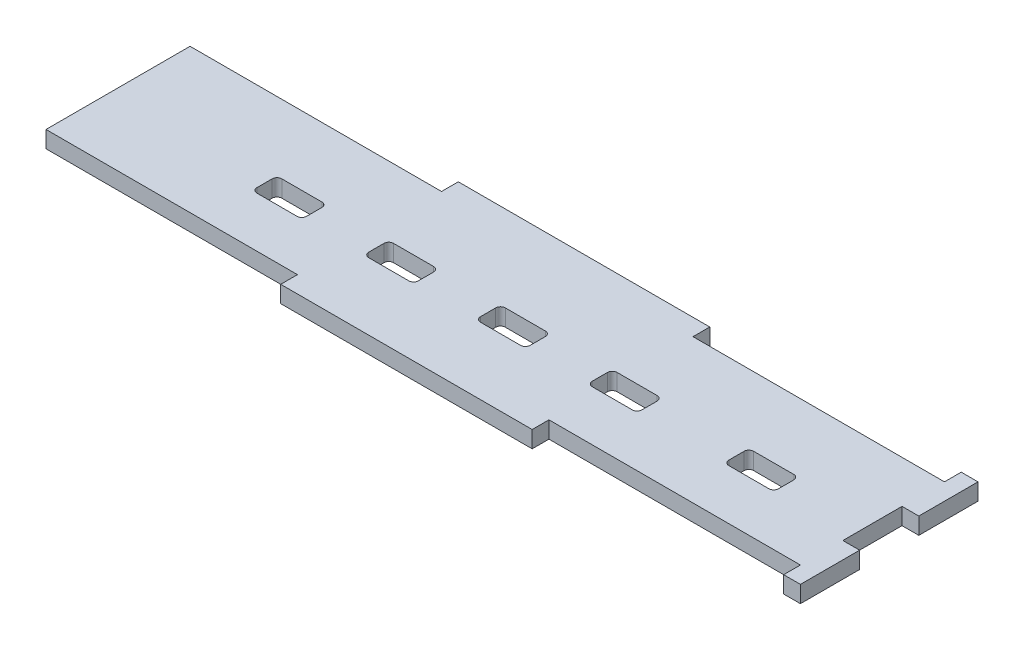
SolidWorks part; units mm, degrees
ref_plane "Front Plane" through (0, 0, 0) normal (0, 0, 1) x (1, 0, 0)
ref_plane "Top Plane" through (0, 0, 0) normal (0, 1, 0) x (1, 0, 0)
ref_plane "Right Plane" through (0, 0, 0) normal (1, 0, 0) x (0, 0, -1)
sketch "Sketch1" plane through (0, 0, 0) normal (0, 1, 0) x (1, 0, 0)
  line L6 (4, 2.8333) -> (4, 12.3667)
  line L8 (-117.5, 12.3667) -> (-117.5, 2.8333)
  line L11 (6.7, -6.7) -> (4, -6.7)
  line L12 (-117.5, 19.2) -> (-117.5, 12.3667)
  line L17 (6.7, -6.7) -> (6.7, 2.8333)
  line L18 (-117.5, -4) -> (-117.5, 2.8333)
  line L21 (-111.5, -4) -> (-117.5, -4) construction
  line L22 (4, -4) -> (-111.5, -4) construction
  line L23 (-117.5, -4) -> (-77, -4)
  line L25 (-120.2, 21.9) -> (-120.2, -6.7) construction
  line L28 (-36.5, -4) -> (4, -4)
  line L31 (-77, -4) -> (-77, -6.7)
  line L32 (-36.5, -4) -> (-36.5, -6.7)
  line L35 (-117.5, 19.2) -> (-117.5, -4) construction
  line L36 (-111.5, -6.7) -> (-120.2, -6.7) construction
  line L37 (6.7, -6.7) -> (-111.5, -6.7) construction
  line L39 (6.7, -6.7) -> (6.7, 21.9) construction
  line L40 (6.7, 12.3667) -> (6.7, 21.9)
  line L41 (6.7, 12.3667) -> (4, 12.3667)
  line L42 (6.7, 2.8333) -> (4, 2.8333)
  line L43 (4, -4) -> (4, -6.7)
  line L44 (4, 19.2) -> (4, 21.9)
  line L45 (4, -4) -> (4, 19.2) construction
  line L46 (-36.5, -6.7) -> (-77, -6.7)
  line L47 (4, 19.2) -> (-111.5, 19.2) construction
  line L48 (-111.5, 19.2) -> (-117.5, 19.2) construction
  line L49 (6.7, 21.9) -> (-111.5, 21.9) construction
  line L50 (-111.5, 21.9) -> (-120.2, 21.9) construction
  line L52 (6.7, 21.9) -> (4, 21.9)
  line L54 (-36.5, 19.2) -> (4, 19.2)
  line L55 (-36.5, 19.2) -> (-36.5, 21.9)
  line L56 (-36.5, 21.9) -> (-77, 21.9)
  line L57 (-77, 19.2) -> (-77, 21.9)
  line L58 (-117.5, 19.2) -> (-77, 19.2)
  line L59 (-91.6279, 8.1) -> (-85.1721, 8.1)
  line L60 (-92.4, 7.3279) -> (-92.4, 4.8721)
  line L61 (-91.6279, 4.1) -> (-85.1721, 4.1)
  line L62 (-84.4, 7.3279) -> (-84.4, 4.8721)
  line L63 (-92.4, 8.1) -> (-84.4, 4.1) construction
  line L64 (-92.4, 4.1) -> (-84.4, 8.1) construction
  line L65 (-73.6279, 8.1) -> (-67.1721, 8.1)
  line L66 (-74.4, 7.3279) -> (-74.4, 4.8721)
  line L67 (-73.6279, 4.1) -> (-67.1721, 4.1)
  line L68 (-66.4, 7.3279) -> (-66.4, 4.8721)
  line L69 (-74.4, 8.1) -> (-66.4, 4.1) construction
  line L70 (-74.4, 4.1) -> (-66.4, 8.1) construction
  line L71 (-55.6279, 8.1) -> (-49.1721, 8.1)
  line L72 (-56.4, 7.3279) -> (-56.4, 4.8721)
  line L73 (-55.6279, 4.1) -> (-49.1721, 4.1)
  line L74 (-48.4, 7.3279) -> (-48.4, 4.8721)
  line L75 (-56.4, 8.1) -> (-48.4, 4.1) construction
  line L76 (-56.4, 4.1) -> (-48.4, 8.1) construction
  line L77 (-37.6279, 8.1) -> (-31.1721, 8.1)
  line L78 (-38.4, 7.3279) -> (-38.4, 4.8721)
  line L79 (-37.6279, 4.1) -> (-31.1721, 4.1)
  line L80 (-30.4, 7.3279) -> (-30.4, 4.8721)
  line L81 (-38.4, 8.1) -> (-30.4, 4.1) construction
  line L82 (-38.4, 4.1) -> (-30.4, 8.1) construction
  line L83 (-15.6279, 8.1) -> (-9.1721, 8.1)
  line L84 (-16.4, 7.3279) -> (-16.4, 4.8721)
  line L85 (-15.6279, 4.1) -> (-9.1721, 4.1)
  line L86 (-8.4, 7.3279) -> (-8.4, 4.8721)
  line L87 (-16.4, 8.1) -> (-8.4, 4.1) construction
  line L88 (-16.4, 4.1) -> (-8.4, 8.1) construction
  arc A3 (-8.4, 4.8721) -> (-9.1721, 4.1) centre (-9.1721, 4.8721) cw
  arc A4 (-15.6279, 4.1) -> (-16.4, 4.8721) centre (-15.6279, 4.8721) cw
  arc A5 (-16.4, 7.3279) -> (-15.6279, 8.1) centre (-15.6279, 7.3279) cw
  arc A6 (-9.1721, 8.1) -> (-8.4, 7.3279) centre (-9.1721, 7.3279) cw
  arc A7 (-30.4, 7.3279) -> (-31.1721, 8.1) centre (-31.1721, 7.3279) ccw
  arc A8 (-37.6279, 8.1) -> (-38.4, 7.3279) centre (-37.6279, 7.3279) ccw
  arc A9 (-38.4, 4.8721) -> (-37.6279, 4.1) centre (-37.6279, 4.8721) ccw
  arc A10 (-31.1721, 4.1) -> (-30.4, 4.8721) centre (-31.1721, 4.8721) ccw
  arc A11 (-49.1721, 8.1) -> (-48.4, 7.3279) centre (-49.1721, 7.3279) cw
  arc A12 (-48.4, 4.8721) -> (-49.1721, 4.1) centre (-49.1721, 4.8721) cw
  arc A13 (-55.6279, 4.1) -> (-56.4, 4.8721) centre (-55.6279, 4.8721) cw
  arc A14 (-56.4, 7.3279) -> (-55.6279, 8.1) centre (-55.6279, 7.3279) cw
  arc A15 (-67.1721, 8.1) -> (-66.4, 7.3279) centre (-67.1721, 7.3279) cw
  arc A16 (-66.4, 4.8721) -> (-67.1721, 4.1) centre (-67.1721, 4.8721) cw
  arc A17 (-73.6279, 4.1) -> (-74.4, 4.8721) centre (-73.6279, 4.8721) cw
  arc A18 (-74.4, 7.3279) -> (-73.6279, 8.1) centre (-73.6279, 7.3279) cw
  arc A19 (-85.1721, 8.1) -> (-84.4, 7.3279) centre (-85.1721, 7.3279) cw
  arc A20 (-84.4, 4.8721) -> (-85.1721, 4.1) centre (-85.1721, 4.8721) cw
  arc A21 (-91.6279, 4.1) -> (-92.4, 4.8721) centre (-91.6279, 4.8721) cw
  arc A22 (-91.6279, 8.1) -> (-92.4, 7.3279) centre (-91.6279, 7.3279) ccw
  point P5 (-88.4, 6.1)
  point P7 (-12.4, 6.1)
  point P8 (-52.4, 6.1)
  point P9 (-34.4, 6.1)
  point P10 (-70.4, 6.1)
  point P11 (-88.4, 6.1)
  point P21 (-70.4, 6.1)
  point P52 (-52.4, 6.1)
  point P57 (-34.4, 6.1)
  point P62 (-12.4, 6.1)
  dimension "D9" = 8
  dimension "D13" = 4
  dimension "D19" = 0.7721
  dimension "D2" = 8
  dimension "D4" = 8
  dimension "D10" = 8
  dimension "D12" = 8
  dimension "D14" = 4
  dimension "D16" = 4
  dimension "D17" = 4
  dimension "D18" = 4
  dimension "D15" = 2.7
extrude "Boss-Extrude1" add sketch "Sketch1" along normal blind 2.7
